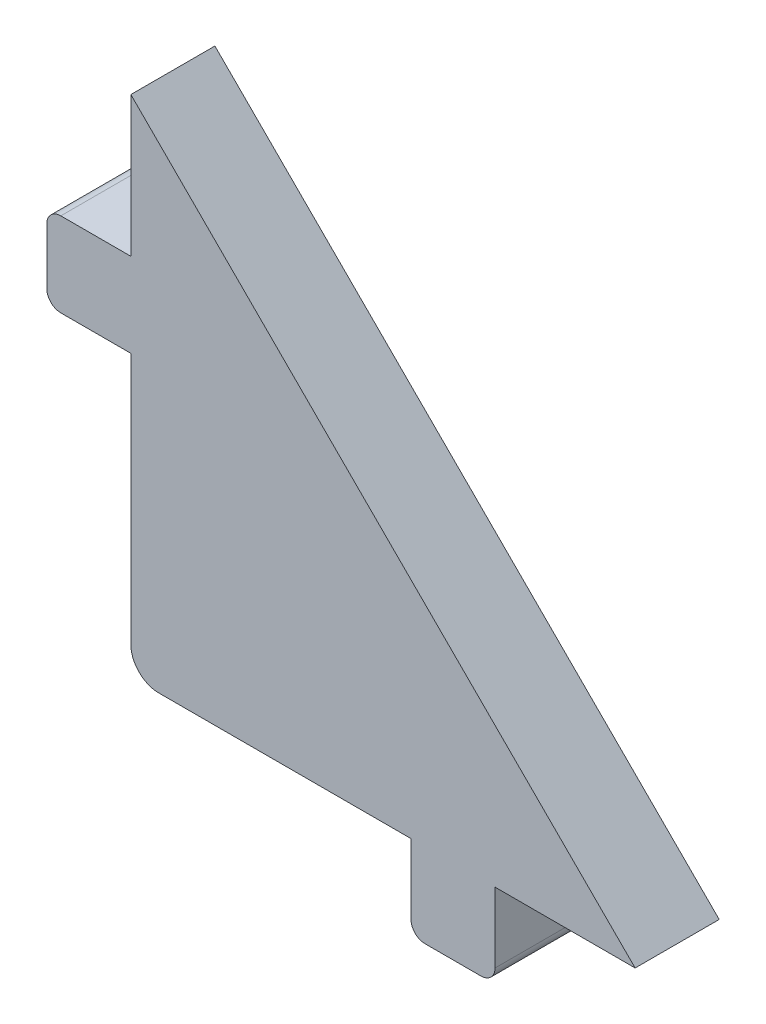
SolidWorks part; units mm, degrees
ref_plane "Спереди" through (0, 0, 0) normal (0, 0, 1) x (1, 0, 0)
ref_plane "Сверху" through (0, 0, 0) normal (0, 1, 0) x (1, 0, 0)
ref_plane "Справа" through (0, 0, 0) normal (1, 0, 0) x (0, 0, -1)
sketch "Эскиз1" plane through (0, 0, 0) normal (0, 0, 1) x (1, 0, 0)
  line L0 (0, 0) -> (0, 3)
  line L1 (0, 3) -> (8, 3)
  line L2 (8, 3) -> (16, -5)
  line L3 (16, -5) -> (16, -13)
  line L4 (16, -13) -> (13, -13)
  line L5 (13, -13) -> (13, -10)
  line L6 (13, -10) -> (3, -10)
  line L7 (3, -10) -> (3, 0)
  line L8 (3, 0) -> (0, 0)
  line L9 (8, 3) -> (3, 8)
  line L10 (3, 8) -> (3, 3)
  line L11 (16, -10) -> (21, -10)
  line L12 (21, -10) -> (16, -5)
  dimension "D1" = 3
  dimension "D2" = 10
  dimension "D3" = 45
  dimension "D4" = 5
extrude "Бобышка-Вытянуть1" add sketch "Эскиз1" along normal blind 3 contours L8 L7 L6 L5 L4 L3 L2 L1 L0 | L9 L10 L1 | L11 L12 L3
fillet "Скругление1" radius 0.5 4 edges at (0, 3, 1.5) (0, 0, 1.5) (13, -13, 1.5) (16, -13, 1.5)
fillet "Скругление2" radius 1 1 edges at (3, -10, 1.5)
